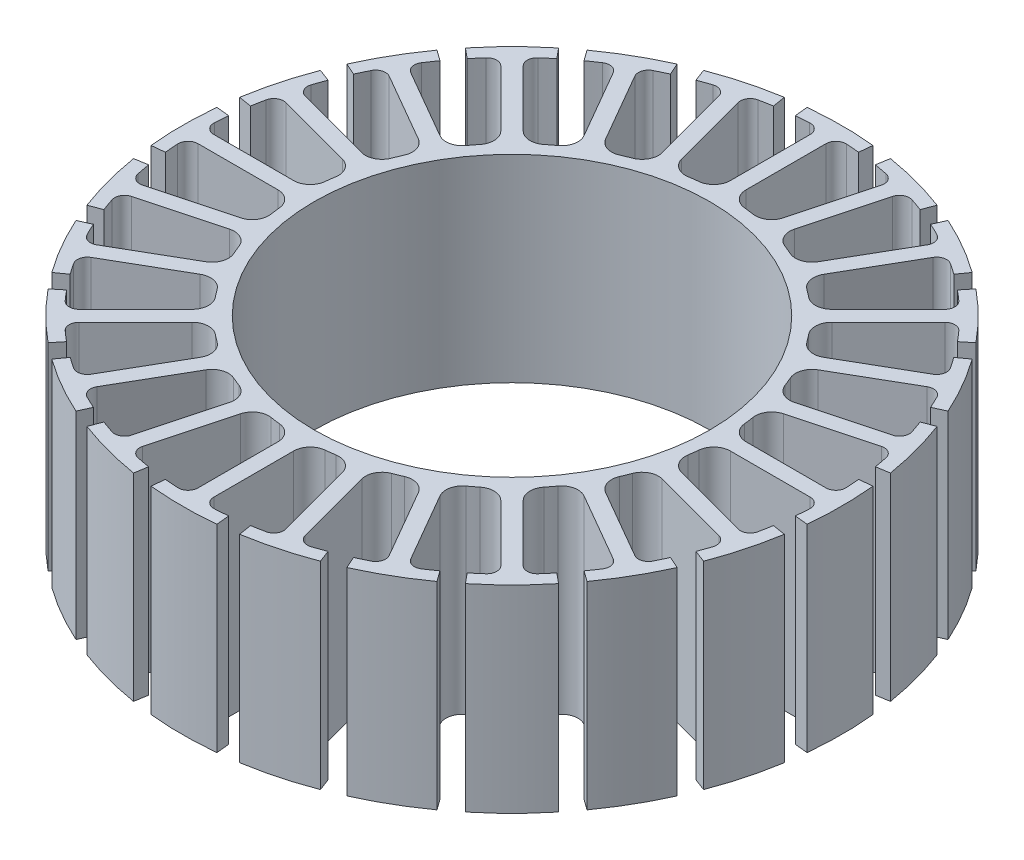
SolidWorks part; units mm, degrees
ref_plane "Ön Düzlem" through (0, 0, 0) normal (0, 0, 1) x (1, 0, 0)
ref_plane "Üst Düzlem" through (0, 0, 0) normal (0, 1, 0) x (1, 0, 0)
ref_plane "Sağ Düzlem" through (0, 0, 0) normal (1, 0, 0) x (0, 0, -1)
sketch "Çizim1" plane through (0, 0, 0) normal (0, 1, 0) x (1, 0, 0)
  line L0 (-2.4, 23.8797) -> (-2.5, 24.8747)
  line L5 (3.8623, 23.6872) -> (4.0232, 24.6741)
  line L6 (-0.6, 23.2108) -> (-0.6, 17.1505)
  line L7 (2.4, 23.8797) -> (2.5, 24.8747)
  line L8 (0.6, 23.2108) -> (0.6, 17.1505)
  line L9 (5.4278, 22.5752) -> (3.8593, 16.7214)
  line L10 (8.4987, 22.4449) -> (8.8529, 23.3801)
  line L11 (6.5869, 22.2646) -> (5.0184, 16.4108)
  line L12 (9.8614, 21.8804) -> (10.2723, 22.7921)
  line L13 (11.0858, 20.4011) -> (8.0556, 15.1528)
  line L14 (14.0183, 19.4804) -> (14.6024, 20.2921)
  line L15 (12.125, 19.8011) -> (9.0949, 14.5528)
  line L16 (15.1884, 18.5826) -> (15.8213, 19.3568)
  line L17 (15.9882, 16.8368) -> (11.703, 12.5515)
  line L18 (18.5826, 15.1884) -> (19.3568, 15.8213)
  line L19 (16.8368, 15.9882) -> (12.5515, 11.703)
  line L20 (19.4804, 14.0183) -> (20.2921, 14.6024)
  line L21 (19.8011, 12.125) -> (14.5528, 9.0949)
  line L22 (21.8804, 9.8614) -> (22.7921, 10.2723)
  line L23 (20.4011, 11.0858) -> (15.1528, 8.0556)
  line L24 (22.4449, 8.4987) -> (23.3801, 8.8529)
  line L25 (22.2646, 6.5869) -> (16.4108, 5.0184)
  line L26 (23.6872, 3.8623) -> (24.6741, 4.0232)
  line L27 (22.5752, 5.4278) -> (16.7214, 3.8593)
  line L28 (23.8797, 2.4) -> (24.8747, 2.5)
  line L29 (23.2108, 0.6) -> (17.1505, 0.6)
  line L30 (23.8797, -2.4) -> (24.8747, -2.5)
  line L31 (23.2108, -0.6) -> (17.1505, -0.6)
  line L32 (23.6872, -3.8623) -> (24.6741, -4.0232)
  line L33 (22.5752, -5.4278) -> (16.7214, -3.8593)
  line L34 (22.4449, -8.4987) -> (23.3801, -8.8529)
  line L35 (22.2646, -6.5869) -> (16.4108, -5.0184)
  line L36 (21.8804, -9.8614) -> (22.7921, -10.2723)
  line L37 (20.4011, -11.0858) -> (15.1528, -8.0556)
  line L38 (19.4804, -14.0183) -> (20.2921, -14.6024)
  line L39 (19.8011, -12.125) -> (14.5528, -9.0949)
  line L40 (18.5826, -15.1884) -> (19.3568, -15.8213)
  line L41 (16.8368, -15.9882) -> (12.5515, -11.703)
  line L42 (15.1884, -18.5826) -> (15.8213, -19.3568)
  line L43 (15.9882, -16.8368) -> (11.703, -12.5515)
  line L44 (14.0183, -19.4804) -> (14.6024, -20.2921)
  line L45 (12.125, -19.8011) -> (9.0949, -14.5528)
  line L46 (9.8614, -21.8804) -> (10.2723, -22.7921)
  line L47 (11.0858, -20.4011) -> (8.0556, -15.1528)
  line L48 (8.4987, -22.4449) -> (8.8529, -23.3801)
  line L49 (6.5869, -22.2646) -> (5.0184, -16.4108)
  line L50 (3.8623, -23.6872) -> (4.0232, -24.6741)
  line L51 (5.4278, -22.5752) -> (3.8593, -16.7214)
  line L52 (2.4, -23.8797) -> (2.5, -24.8747)
  line L53 (0.6, -23.2108) -> (0.6, -17.1505)
  line L54 (-2.4, -23.8797) -> (-2.5, -24.8747)
  line L55 (-0.6, -23.2108) -> (-0.6, -17.1505)
  line L56 (-3.8623, -23.6872) -> (-4.0232, -24.6741)
  line L57 (-5.4278, -22.5752) -> (-3.8593, -16.7214)
  line L58 (-8.4987, -22.4449) -> (-8.8529, -23.3801)
  line L59 (-6.5869, -22.2646) -> (-5.0184, -16.4108)
  line L60 (-9.8614, -21.8804) -> (-10.2723, -22.7921)
  line L61 (-11.0858, -20.4011) -> (-8.0556, -15.1528)
  line L62 (-14.0183, -19.4804) -> (-14.6024, -20.2921)
  line L63 (-12.125, -19.8011) -> (-9.0949, -14.5528)
  line L64 (-15.1884, -18.5826) -> (-15.8213, -19.3568)
  line L65 (-15.9882, -16.8368) -> (-11.703, -12.5515)
  line L66 (-18.5826, -15.1884) -> (-19.3568, -15.8213)
  line L67 (-16.8368, -15.9882) -> (-12.5515, -11.703)
  line L68 (-19.4804, -14.0183) -> (-20.2921, -14.6024)
  line L69 (-19.8011, -12.125) -> (-14.5528, -9.0949)
  line L70 (-21.8804, -9.8614) -> (-22.7921, -10.2723)
  line L71 (-20.4011, -11.0858) -> (-15.1528, -8.0556)
  line L72 (-22.4449, -8.4987) -> (-23.3801, -8.8529)
  line L73 (-22.2646, -6.5869) -> (-16.4108, -5.0184)
  line L74 (-23.6872, -3.8623) -> (-24.6741, -4.0232)
  line L75 (-22.5752, -5.4278) -> (-16.7214, -3.8593)
  line L76 (-23.8797, -2.4) -> (-24.8747, -2.5)
  line L77 (-23.2108, -0.6) -> (-17.1505, -0.6)
  line L78 (-23.8797, 2.4) -> (-24.8747, 2.5)
  line L79 (-23.2108, 0.6) -> (-17.1505, 0.6)
  line L80 (-23.6872, 3.8623) -> (-24.6741, 4.0232)
  line L81 (-22.5752, 5.4278) -> (-16.7214, 3.8593)
  line L82 (-22.4449, 8.4987) -> (-23.3801, 8.8529)
  line L83 (-22.2646, 6.5869) -> (-16.4108, 5.0184)
  line L84 (-21.8804, 9.8614) -> (-22.7921, 10.2723)
  line L85 (-20.4011, 11.0858) -> (-15.1528, 8.0556)
  line L86 (-19.4804, 14.0183) -> (-20.2921, 14.6024)
  line L87 (-19.8011, 12.125) -> (-14.5528, 9.0949)
  line L88 (-18.5826, 15.1884) -> (-19.3568, 15.8213)
  line L89 (-16.8368, 15.9882) -> (-12.5515, 11.703)
  line L90 (-15.1884, 18.5826) -> (-15.8213, 19.3568)
  line L91 (-15.9882, 16.8368) -> (-11.703, 12.5515)
  line L92 (-14.0183, 19.4804) -> (-14.6024, 20.2921)
  line L93 (-12.125, 19.8011) -> (-9.0949, 14.5528)
  line L94 (-9.8614, 21.8804) -> (-10.2723, 22.7921)
  line L95 (-11.0858, 20.4011) -> (-8.0556, 15.1528)
  line L96 (-8.4987, 22.4449) -> (-8.8529, 23.3801)
  line L97 (-6.5869, 22.2646) -> (-5.0184, 16.4108)
  line L98 (-3.8623, 23.6872) -> (-4.0232, 24.6741)
  line L99 (-5.4278, 22.5752) -> (-3.8593, 16.7214)
  line L100 (0, 14.1356) -> (0, 41.1871) construction
  arc A0 (2.5, 24.8747) -> (-2.5, 24.8747) centre (0, 0) ccw
  arc A1 (-1.3935, 23.9595) -> (-2.4, 23.8797) centre (0, 0) ccw
  arc A2 (-1.7159, 15.9077) -> (-2.4597, 15.8098) centre (0, 0) ccw
  arc A3 (2.4, 23.8797) -> (1.3935, 23.9595) centre (0, 0) ccw
  arc A4 (8.8529, 23.3801) -> (4.0232, 24.6741) centre (0, 0) ccw
  arc A5 (4.8551, 23.5038) -> (3.8623, 23.6872) centre (0, 0) ccw
  arc A6 (8.4987, 22.4449) -> (7.5472, 22.7824) centre (0, 0) ccw
  arc A7 (14.6024, 20.2921) -> (10.2723, 22.7921) centre (0, 0) ccw
  arc A8 (10.7729, 21.4463) -> (9.8614, 21.8804) centre (0, 0) ccw
  arc A9 (14.0183, 19.4804) -> (13.1866, 20.0528) centre (0, 0) ccw
  arc A10 (19.3568, 15.8213) -> (15.8213, 19.3568) centre (0, 0) ccw
  arc A11 (15.9565, 17.9273) -> (15.1884, 18.5826) centre (0, 0) ccw
  arc A12 (18.5826, 15.1884) -> (17.9273, 15.9565) centre (0, 0) ccw
  arc A13 (22.7921, 10.2723) -> (20.2921, 14.6024) centre (0, 0) ccw
  arc A14 (20.0528, 13.1866) -> (19.4804, 14.0183) centre (0, 0) ccw
  arc A15 (21.8804, 9.8614) -> (21.4463, 10.7729) centre (0, 0) ccw
  arc A16 (24.6741, 4.0232) -> (23.3801, 8.8529) centre (0, 0) ccw
  arc A17 (22.7824, 7.5472) -> (22.4449, 8.4987) centre (0, 0) ccw
  arc A18 (23.6872, 3.8623) -> (23.5038, 4.8551) centre (0, 0) ccw
  arc A19 (24.8747, -2.5) -> (24.8747, 2.5) centre (0, 0) ccw
  arc A20 (23.9595, 1.3935) -> (23.8797, 2.4) centre (0, 0) ccw
  arc A21 (23.8797, -2.4) -> (23.9595, -1.3935) centre (0, 0) ccw
  arc A22 (23.3801, -8.8529) -> (24.6741, -4.0232) centre (0, 0) ccw
  arc A23 (23.5038, -4.8551) -> (23.6872, -3.8623) centre (0, 0) ccw
  arc A24 (22.4449, -8.4987) -> (22.7824, -7.5472) centre (0, 0) ccw
  arc A25 (20.2921, -14.6024) -> (22.7921, -10.2723) centre (0, 0) ccw
  arc A26 (21.4463, -10.7729) -> (21.8804, -9.8614) centre (0, 0) ccw
  arc A27 (19.4804, -14.0183) -> (20.0528, -13.1866) centre (0, 0) ccw
  arc A28 (15.8213, -19.3568) -> (19.3568, -15.8213) centre (0, 0) ccw
  arc A29 (17.9273, -15.9565) -> (18.5826, -15.1884) centre (0, 0) ccw
  arc A30 (15.1884, -18.5826) -> (15.9565, -17.9273) centre (0, 0) ccw
  arc A31 (10.2723, -22.7921) -> (14.6024, -20.2921) centre (0, 0) ccw
  arc A32 (13.1866, -20.0528) -> (14.0183, -19.4804) centre (0, 0) ccw
  arc A33 (9.8614, -21.8804) -> (10.7729, -21.4463) centre (0, 0) ccw
  arc A34 (4.0232, -24.6741) -> (8.8529, -23.3801) centre (0, 0) ccw
  arc A35 (7.5472, -22.7824) -> (8.4987, -22.4449) centre (0, 0) ccw
  arc A36 (3.8623, -23.6872) -> (4.8551, -23.5038) centre (0, 0) ccw
  arc A37 (-2.5, -24.8747) -> (2.5, -24.8747) centre (0, 0) ccw
  arc A38 (1.3935, -23.9595) -> (2.4, -23.8797) centre (0, 0) ccw
  arc A39 (-2.4, -23.8797) -> (-1.3935, -23.9595) centre (0, 0) ccw
  arc A40 (-8.8529, -23.3801) -> (-4.0232, -24.6741) centre (0, 0) ccw
  arc A41 (-4.8551, -23.5038) -> (-3.8623, -23.6872) centre (0, 0) ccw
  arc A42 (-8.4987, -22.4449) -> (-7.5472, -22.7824) centre (0, 0) ccw
  arc A43 (-14.6024, -20.2921) -> (-10.2723, -22.7921) centre (0, 0) ccw
  arc A44 (-10.7729, -21.4463) -> (-9.8614, -21.8804) centre (0, 0) ccw
  arc A45 (-14.0183, -19.4804) -> (-13.1866, -20.0528) centre (0, 0) ccw
  arc A46 (-19.3568, -15.8213) -> (-15.8213, -19.3568) centre (0, 0) ccw
  arc A47 (-15.9565, -17.9273) -> (-15.1884, -18.5826) centre (0, 0) ccw
  arc A48 (-18.5826, -15.1884) -> (-17.9273, -15.9565) centre (0, 0) ccw
  arc A49 (-22.7921, -10.2723) -> (-20.2921, -14.6024) centre (0, 0) ccw
  arc A50 (-20.0528, -13.1866) -> (-19.4804, -14.0183) centre (0, 0) ccw
  arc A51 (-21.8804, -9.8614) -> (-21.4463, -10.7729) centre (0, 0) ccw
  arc A52 (-24.6741, -4.0232) -> (-23.3801, -8.8529) centre (0, 0) ccw
  arc A53 (-22.7824, -7.5472) -> (-22.4449, -8.4987) centre (0, 0) ccw
  arc A54 (-23.6872, -3.8623) -> (-23.5038, -4.8551) centre (0, 0) ccw
  arc A55 (-24.8747, 2.5) -> (-24.8747, -2.5) centre (0, 0) ccw
  arc A56 (-23.9595, -1.3935) -> (-23.8797, -2.4) centre (0, 0) ccw
  arc A57 (-23.8797, 2.4) -> (-23.9595, 1.3935) centre (0, 0) ccw
  arc A58 (-23.3801, 8.8529) -> (-24.6741, 4.0232) centre (0, 0) ccw
  arc A59 (-23.5038, 4.8551) -> (-23.6872, 3.8623) centre (0, 0) ccw
  arc A60 (-22.4449, 8.4987) -> (-22.7824, 7.5472) centre (0, 0) ccw
  arc A61 (-20.2921, 14.6024) -> (-22.7921, 10.2723) centre (0, 0) ccw
  arc A62 (-21.4463, 10.7729) -> (-21.8804, 9.8614) centre (0, 0) ccw
  arc A63 (-19.4804, 14.0183) -> (-20.0528, 13.1866) centre (0, 0) ccw
  arc A64 (-15.8213, 19.3568) -> (-19.3568, 15.8213) centre (0, 0) ccw
  arc A65 (-17.9273, 15.9565) -> (-18.5826, 15.1884) centre (0, 0) ccw
  arc A66 (-15.1884, 18.5826) -> (-15.9565, 17.9273) centre (0, 0) ccw
  arc A67 (-10.2723, 22.7921) -> (-14.6024, 20.2921) centre (0, 0) ccw
  arc A68 (-13.1866, 20.0528) -> (-14.0183, 19.4804) centre (0, 0) ccw
  arc A69 (-9.8614, 21.8804) -> (-10.7729, 21.4463) centre (0, 0) ccw
  arc A70 (-4.0232, 24.6741) -> (-8.8529, 23.3801) centre (0, 0) ccw
  arc A71 (-7.5472, 22.7824) -> (-8.4987, 22.4449) centre (0, 0) ccw
  arc A72 (-3.8623, 23.6872) -> (-4.8551, 23.5038) centre (0, 0) ccw
  arc A73 (11.0858, 20.4011) -> (10.7729, 21.4463) centre (10.4363, 20.7761) ccw
  arc A74 (12.125, 19.8011) -> (13.1866, 20.0528) centre (12.7745, 19.4261) cw
  arc A75 (15.9882, 16.8368) -> (15.9565, 17.9273) centre (15.4579, 17.3671) ccw
  arc A76 (16.8368, 15.9882) -> (17.9273, 15.9565) centre (17.3671, 15.4579) cw
  arc A77 (19.8011, 12.125) -> (20.0528, 13.1866) centre (19.4261, 12.7745) ccw
  arc A78 (20.4011, 11.0858) -> (21.4463, 10.7729) centre (20.7761, 10.4363) cw
  arc A79 (22.2646, 6.5869) -> (22.7824, 7.5472) centre (22.0705, 7.3114) ccw
  arc A80 (22.5752, 5.4278) -> (23.5038, 4.8551) centre (22.7693, 4.7034) cw
  arc A81 (23.2108, 0.6) -> (23.9595, 1.3935) centre (23.2108, 1.35) ccw
  arc A82 (23.2108, -0.6) -> (23.9595, -1.3935) centre (23.2108, -1.35) cw
  arc A83 (22.5752, -5.4278) -> (23.5038, -4.8551) centre (22.7693, -4.7034) ccw
  arc A84 (22.2646, -6.5869) -> (22.7824, -7.5472) centre (22.0705, -7.3114) cw
  arc A85 (20.4011, -11.0858) -> (21.4463, -10.7729) centre (20.7761, -10.4363) ccw
  arc A86 (19.8011, -12.125) -> (20.0528, -13.1866) centre (19.4261, -12.7745) cw
  arc A87 (16.8368, -15.9882) -> (17.9273, -15.9565) centre (17.3671, -15.4579) ccw
  arc A88 (15.9882, -16.8368) -> (15.9565, -17.9273) centre (15.4579, -17.3671) cw
  arc A89 (12.125, -19.8011) -> (13.1866, -20.0528) centre (12.7745, -19.4261) ccw
  arc A90 (11.0858, -20.4011) -> (10.7729, -21.4463) centre (10.4363, -20.7761) cw
  arc A91 (6.5869, -22.2646) -> (7.5472, -22.7824) centre (7.3114, -22.0705) ccw
  arc A92 (5.4278, -22.5752) -> (4.8551, -23.5038) centre (4.7034, -22.7693) cw
  arc A93 (0.6, -23.2108) -> (1.3935, -23.9595) centre (1.35, -23.2108) ccw
  arc A94 (-0.6, -23.2108) -> (-1.3935, -23.9595) centre (-1.35, -23.2108) cw
  arc A95 (-5.4278, -22.5752) -> (-4.8551, -23.5038) centre (-4.7034, -22.7693) ccw
  arc A96 (-6.5869, -22.2646) -> (-7.5472, -22.7824) centre (-7.3114, -22.0705) cw
  arc A97 (-11.0858, -20.4011) -> (-10.7729, -21.4463) centre (-10.4363, -20.7761) ccw
  arc A98 (-12.125, -19.8011) -> (-13.1866, -20.0528) centre (-12.7745, -19.4261) cw
  arc A99 (-15.9882, -16.8368) -> (-15.9565, -17.9273) centre (-15.4579, -17.3671) ccw
  arc A100 (-16.8368, -15.9882) -> (-17.9273, -15.9565) centre (-17.3671, -15.4579) cw
  arc A101 (-19.8011, -12.125) -> (-20.0528, -13.1866) centre (-19.4261, -12.7745) ccw
  arc A102 (-20.4011, -11.0858) -> (-21.4463, -10.7729) centre (-20.7761, -10.4363) cw
  arc A103 (-22.2646, -6.5869) -> (-22.7824, -7.5472) centre (-22.0705, -7.3114) ccw
  arc A104 (-22.5752, -5.4278) -> (-23.5038, -4.8551) centre (-22.7693, -4.7034) cw
  arc A105 (-23.2108, -0.6) -> (-23.9595, -1.3935) centre (-23.2108, -1.35) ccw
  arc A106 (-23.2108, 0.6) -> (-23.9595, 1.3935) centre (-23.2108, 1.35) cw
  arc A107 (-22.5752, 5.4278) -> (-23.5038, 4.8551) centre (-22.7693, 4.7034) ccw
  arc A108 (-22.2646, 6.5869) -> (-22.7824, 7.5472) centre (-22.0705, 7.3114) cw
  arc A109 (-20.4011, 11.0858) -> (-21.4463, 10.7729) centre (-20.7761, 10.4363) ccw
  arc A110 (-19.8011, 12.125) -> (-20.0528, 13.1866) centre (-19.4261, 12.7745) cw
  arc A111 (-16.8368, 15.9882) -> (-17.9273, 15.9565) centre (-17.3671, 15.4579) ccw
  arc A112 (-15.9882, 16.8368) -> (-15.9565, 17.9273) centre (-15.4579, 17.3671) cw
  arc A113 (-12.125, 19.8011) -> (-13.1866, 20.0528) centre (-12.7745, 19.4261) ccw
  arc A114 (-11.0858, 20.4011) -> (-10.7729, 21.4463) centre (-10.4363, 20.7761) cw
  arc A115 (-6.5869, 22.2646) -> (-7.5472, 22.7824) centre (-7.3114, 22.0705) ccw
  arc A116 (-5.4278, 22.5752) -> (-4.8551, 23.5038) centre (-4.7034, 22.7693) cw
  arc A117 (6.5869, 22.2646) -> (7.5472, 22.7824) centre (7.3114, 22.0705) cw
  arc A118 (5.4278, 22.5752) -> (4.8551, 23.5038) centre (4.7034, 22.7693) ccw
  arc A119 (0.6, 23.2108) -> (1.3935, 23.9595) centre (1.35, 23.2108) cw
  arc A120 (-0.6, 23.2108) -> (-1.3935, 23.9595) centre (-1.35, 23.2108) ccw
  circle A121 centre (0, 0) radius 15
  arc A122 (2.4597, 15.8098) -> (1.7159, 15.9077) centre (0, 0) ccw
  arc A123 (-5.7747, 14.9216) -> (-6.4678, 14.6345) centre (0, 0) ccw
  arc A124 (-9.4399, 12.9185) -> (-10.0351, 12.4618) centre (0, 0) ccw
  arc A125 (-12.4618, 10.0351) -> (-12.9185, 9.4399) centre (0, 0) ccw
  arc A126 (-14.6345, 6.4678) -> (-14.9216, 5.7747) centre (0, 0) ccw
  arc A127 (-15.8098, 2.4597) -> (-15.9077, 1.7159) centre (0, 0) ccw
  arc A128 (-15.9077, -1.7159) -> (-15.8098, -2.4597) centre (0, 0) ccw
  arc A129 (-14.9216, -5.7747) -> (-14.6345, -6.4678) centre (0, 0) ccw
  arc A130 (-12.9185, -9.4399) -> (-12.4618, -10.0351) centre (0, 0) ccw
  arc A131 (-10.0351, -12.4618) -> (-9.4399, -12.9185) centre (0, 0) ccw
  arc A132 (-6.4678, -14.6345) -> (-5.7747, -14.9216) centre (0, 0) ccw
  arc A133 (-2.4597, -15.8098) -> (-1.7159, -15.9077) centre (0, 0) ccw
  arc A134 (1.7159, -15.9077) -> (2.4597, -15.8098) centre (0, 0) ccw
  arc A135 (5.7747, -14.9216) -> (6.4678, -14.6345) centre (0, 0) ccw
  arc A136 (9.4399, -12.9185) -> (10.0351, -12.4618) centre (0, 0) ccw
  arc A137 (12.4618, -10.0351) -> (12.9185, -9.4399) centre (0, 0) ccw
  arc A138 (14.6345, -6.4678) -> (14.9216, -5.7747) centre (0, 0) ccw
  arc A139 (15.8098, -2.4597) -> (15.9077, -1.7159) centre (0, 0) ccw
  arc A140 (15.9077, 1.7159) -> (15.8098, 2.4597) centre (0, 0) ccw
  arc A141 (14.9216, 5.7747) -> (14.6345, 6.4678) centre (0, 0) ccw
  arc A142 (12.9185, 9.4399) -> (12.4618, 10.0351) centre (0, 0) ccw
  arc A143 (10.0351, 12.4618) -> (9.4399, 12.9185) centre (0, 0) ccw
  arc A144 (6.4678, 14.6345) -> (5.7747, 14.9216) centre (0, 0) ccw
  arc A145 (-12.5515, -11.703) -> (-12.4618, -10.0351) centre (-13.4354, -10.8191) ccw
  arc A146 (-14.5528, -9.0949) -> (-12.9185, -9.4399) centre (-13.9278, -10.1774) cw
  arc A147 (-15.1528, -8.0556) -> (-14.6345, -6.4678) centre (-15.7778, -6.9731) ccw
  arc A148 (-16.4108, -5.0184) -> (-14.9216, -5.7747) centre (-16.0873, -6.2258) cw
  arc A149 (-16.7214, -3.8593) -> (-15.8098, -2.4597) centre (-17.0449, -2.6519) ccw
  arc A150 (-17.1505, -0.6) -> (-15.9077, -1.7159) centre (-17.1505, -1.85) cw
  arc A151 (-11.703, -12.5515) -> (-10.0351, -12.4618) centre (-10.8191, -13.4354) cw
  arc A152 (-9.0949, -14.5528) -> (-9.4399, -12.9185) centre (-10.1774, -13.9278) ccw
  arc A153 (-8.0556, -15.1528) -> (-6.4678, -14.6345) centre (-6.9731, -15.7778) cw
  arc A154 (-5.0184, -16.4108) -> (-5.7747, -14.9216) centre (-6.2258, -16.0873) ccw
  arc A155 (-3.8593, -16.7214) -> (-2.4597, -15.8098) centre (-2.6519, -17.0449) cw
  arc A156 (-0.6, -17.1505) -> (-1.7159, -15.9077) centre (-1.85, -17.1505) ccw
  arc A157 (0.6, -17.1505) -> (1.7159, -15.9077) centre (1.85, -17.1505) cw
  arc A158 (3.8593, -16.7214) -> (2.4597, -15.8098) centre (2.6519, -17.0449) ccw
  arc A159 (5.0184, -16.4108) -> (5.7747, -14.9216) centre (6.2258, -16.0873) cw
  arc A160 (8.0556, -15.1528) -> (6.4678, -14.6345) centre (6.9731, -15.7778) ccw
  arc A161 (9.0949, -14.5528) -> (9.4399, -12.9185) centre (10.1774, -13.9278) cw
  arc A162 (11.703, -12.5515) -> (10.0351, -12.4618) centre (10.8191, -13.4354) ccw
  arc A163 (12.5515, -11.703) -> (12.4618, -10.0351) centre (13.4354, -10.8191) cw
  arc A164 (14.5528, -9.0949) -> (12.9185, -9.4399) centre (13.9278, -10.1774) ccw
  arc A165 (15.1528, -8.0556) -> (14.6345, -6.4678) centre (15.7778, -6.9731) cw
  arc A166 (16.4108, -5.0184) -> (14.9216, -5.7747) centre (16.0873, -6.2258) ccw
  arc A167 (16.7214, -3.8593) -> (15.8098, -2.4597) centre (17.0449, -2.6519) cw
  arc A168 (17.1505, -0.6) -> (15.9077, -1.7159) centre (17.1505, -1.85) ccw
  arc A169 (17.1505, 0.6) -> (15.9077, 1.7159) centre (17.1505, 1.85) cw
  arc A170 (16.7214, 3.8593) -> (15.8098, 2.4597) centre (17.0449, 2.6519) ccw
  arc A171 (16.4108, 5.0184) -> (14.9216, 5.7747) centre (16.0873, 6.2258) cw
  arc A172 (15.1528, 8.0556) -> (14.6345, 6.4678) centre (15.7778, 6.9731) ccw
  arc A173 (14.5528, 9.0949) -> (12.9185, 9.4399) centre (13.9278, 10.1774) cw
  arc A174 (12.5515, 11.703) -> (12.4618, 10.0351) centre (13.4354, 10.8191) ccw
  arc A175 (11.703, 12.5515) -> (10.0351, 12.4618) centre (10.8191, 13.4354) cw
  arc A176 (9.0949, 14.5528) -> (9.4399, 12.9185) centre (10.1774, 13.9278) ccw
  arc A177 (8.0556, 15.1528) -> (6.4678, 14.6345) centre (6.9731, 15.7778) cw
  arc A178 (5.0184, 16.4108) -> (5.7747, 14.9216) centre (6.2258, 16.0873) ccw
  arc A179 (3.8593, 16.7214) -> (2.4597, 15.8098) centre (2.6519, 17.0449) cw
  arc A180 (-16.7214, 3.8593) -> (-15.8098, 2.4597) centre (-17.0449, 2.6519) cw
  arc A181 (-17.1505, 0.6) -> (-15.9077, 1.7159) centre (-17.1505, 1.85) ccw
  arc A182 (-16.4108, 5.0184) -> (-14.9216, 5.7747) centre (-16.0873, 6.2258) ccw
  arc A183 (-15.1528, 8.0556) -> (-14.6345, 6.4678) centre (-15.7778, 6.9731) cw
  arc A184 (-14.5528, 9.0949) -> (-12.9185, 9.4399) centre (-13.9278, 10.1774) ccw
  arc A185 (-12.5515, 11.703) -> (-12.4618, 10.0351) centre (-13.4354, 10.8191) cw
  arc A186 (-11.703, 12.5515) -> (-10.0351, 12.4618) centre (-10.8191, 13.4354) ccw
  arc A187 (-9.0949, 14.5528) -> (-9.4399, 12.9185) centre (-10.1774, 13.9278) cw
  arc A188 (-8.0556, 15.1528) -> (-6.4678, 14.6345) centre (-6.9731, 15.7778) ccw
  arc A189 (-5.0184, 16.4108) -> (-5.7747, 14.9216) centre (-6.2258, 16.0873) cw
  arc A190 (-3.8593, 16.7214) -> (-2.4597, 15.8098) centre (-2.6519, 17.0449) ccw
  arc A191 (-0.6, 17.1505) -> (-1.7159, 15.9077) centre (-1.85, 17.1505) cw
  arc A192 (0.6, 17.1505) -> (1.7159, 15.9077) centre (1.85, 17.1505) ccw
  point P4 (0, 26.9663)
  point P7 (6.9794, 26.0474)
  point P24 (13.4831, 23.3535)
  point P33 (19.068, 19.068)
  point P42 (23.3535, 13.4831)
  point P51 (26.0474, 6.9794)
  point P60 (26.9663, 0)
  point P69 (26.0474, -6.9794)
  point P78 (23.3535, -13.4831)
  point P87 (19.068, -19.068)
  point P96 (13.4831, -23.3535)
  point P105 (6.9794, -26.0474)
  point P114 (0, -26.9663)
  point P123 (-6.9794, -26.0474)
  point P132 (-13.4831, -23.3535)
  point P141 (-19.068, -19.068)
  point P150 (-23.3535, -13.4831)
  point P159 (-26.0474, -6.9794)
  point P168 (-26.9663, 0)
  point P177 (-26.0474, 6.9794)
  point P186 (-23.3535, 13.4831)
  point P195 (-19.068, 19.068)
  point P204 (-13.4831, 23.3535)
  point P213 (-6.9794, 26.0474)
  point P222 (0, 0)
  dimension "D1" = 50
  dimension "D2" = 48
  dimension "D4" = 0.75
  dimension "D5" = 30
  dimension "D6" = 1.25
  dimension "D7" = 16
  dimension "D3" = 24
  dimension "D8" = 0.6
  dimension "D9" = 0.6
extrude "Yükseklik-Ekstrüzyon1" add sketch "Çizim1" along normal blind 15
